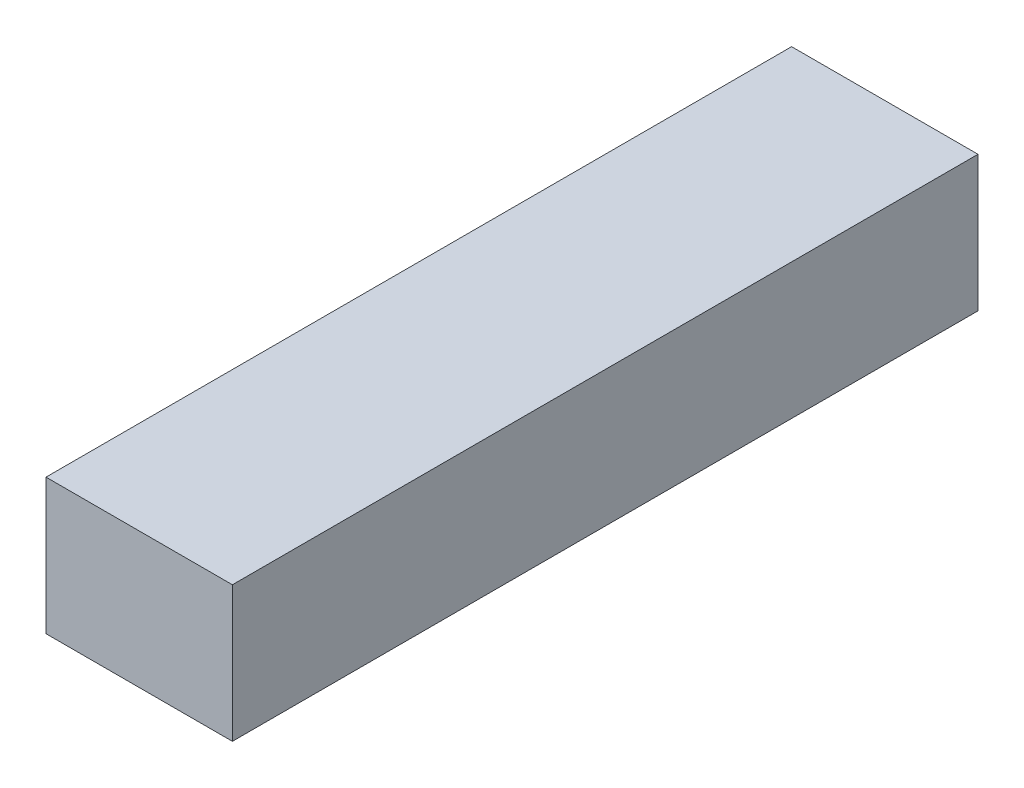
SolidWorks part; units mm, degrees
ref_plane "Front Plane" through (0, 0, 0) normal (0, 0, 1) x (1, 0, 0)
ref_plane "Top Plane" through (0, 0, 0) normal (0, 1, 0) x (1, 0, 0)
ref_plane "Right Plane" through (0, 0, 0) normal (1, 0, 0) x (0, 0, -1)
sketch "Sketch1" plane through (0, 0, 0) normal (0, 0, 1) x (1, 0, 0)
  line L0 (0, 9.15) -> (0, -10.83) construction
  line L1 (-9.75, 0) -> (21.51, 0) construction
  line L3 (3.175, -2.31) -> (-3.175, -2.31)
  line L4 (3.175, -2.31) -> (3.175, 2.31)
  line L5 (3.175, 2.31) -> (-3.175, 2.31)
  line L6 (-3.175, -2.31) -> (-3.175, 2.31)
  line L7 (3.175, -2.31) -> (-3.175, 2.31) construction
  line L8 (3.175, 2.31) -> (-3.175, -2.31) construction
  point P5 (0, 0)
  dimension "D1" = 2.31
  dimension "D2" = 6.35
extrude "Boss-Extrude1" add sketch "Sketch1" along normal blind 25.4
